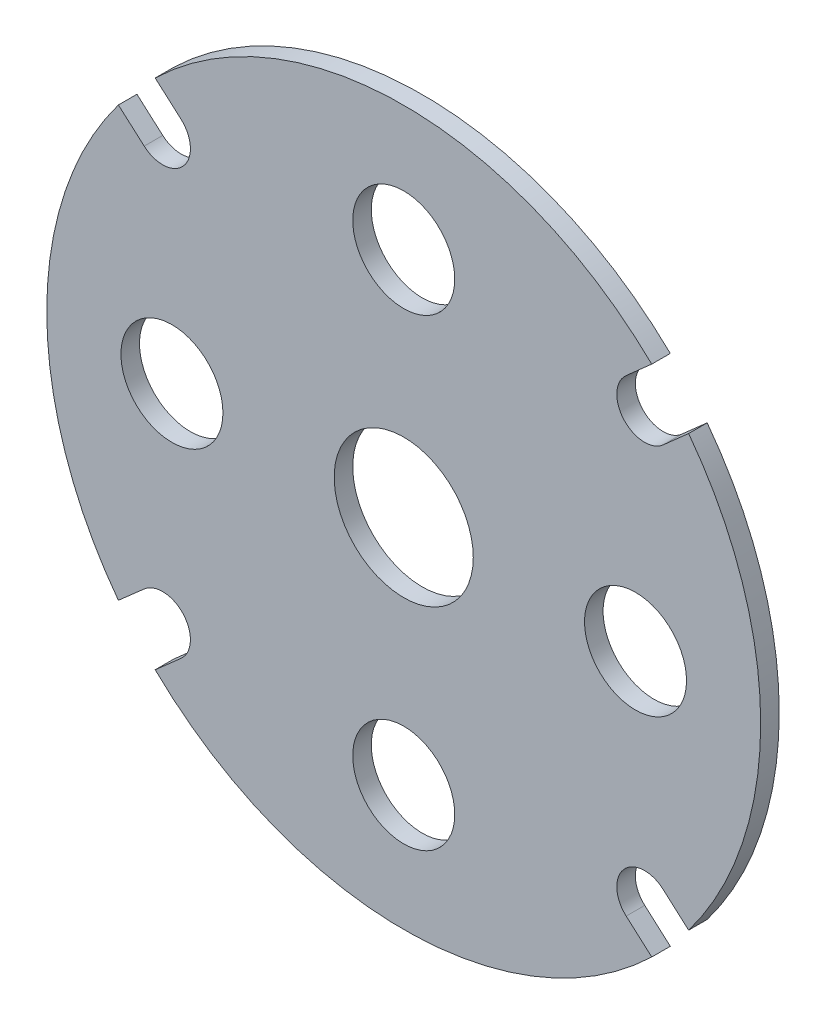
SolidWorks part; units mm, degrees
material "Acrylic (Medium-high impact)"
ref_plane "Front Plane" through (0, 0, 0) normal (0, 0, 1) x (1, 0, 0)
ref_plane "Top Plane" through (0, 0, 0) normal (0, 1, 0) x (1, 0, 0)
ref_plane "Right Plane" through (0, 0, 0) normal (1, 0, 0) x (0, 0, -1)
sketch "Model" plane through (0, 0, 0) normal (0, 0, 1) x (1, 0, 0)
  line L0 (30.7279, -23.1958) -> (27.9693, -20.7537)
  line L1 (26.7508, -27.6884) -> (23.9922, -25.2463)
  line L2 (-30.7735, -23.1353) -> (-27.9907, -20.6815)
  line L3 (-26.8052, -27.6357) -> (-24.0224, -25.1819)
  line L8 (30.7279, 23.1958) -> (27.9693, 20.7537)
  line L9 (26.7508, 27.6884) -> (23.9922, 25.2463)
  line L10 (-30.7735, 23.1353) -> (-27.9907, 20.6815)
  line L11 (-26.8052, 27.6357) -> (-24.0224, 25.1819)
  circle A8 centre (0, 0) radius 7.5
  arc A9 (-26.8052, -27.6357) -> (26.7508, -27.6884) centre (0, 0) ccw
  arc A10 (30.7279, -23.1958) -> (30.7279, 23.1958) centre (0, 0) ccw
  circle A11 centre (-25, 0) radius 5.5
  circle A12 centre (0, 25) radius 5.5
  circle A13 centre (0, -25) radius 5.5
  circle A14 centre (25, 0) radius 5.5
  arc A15 (27.9693, -20.7537) -> (23.9922, -25.2463) centre (25.9808, -23) ccw
  arc A16 (-24.0224, -25.1819) -> (-27.9907, -20.6815) centre (-26.0066, -22.9317) ccw
  arc A26 (23.9922, 25.2463) -> (27.9693, 20.7537) centre (25.9808, 23) ccw
  arc A27 (-27.9907, 20.6815) -> (-24.0224, 25.1819) centre (-26.0066, 22.9317) ccw
  arc A28 (26.7508, 27.6884) -> (-26.8052, 27.6357) centre (0, 0) ccw
  arc A29 (-30.7735, 23.1353) -> (-30.7735, -23.1353) centre (0, 0) ccw
  dimension "D1" = 11
  dimension "D2" = 15
  dimension "D3" = 38.5
  dimension "D4" = 3
  dimension "D5" = 23.9922
  dimension "D6" = 25
  dimension "D7" = 25.9808
  dimension "D8" = 26.7508
  dimension "D9" = 24.0224
  dimension "D10" = 25
  dimension "D11" = 26.0066
  dimension "D12" = 26.8052
  dimension "D13" = 25
  dimension "D14" = 25
extrude "Boss-Extrude1" add sketch "Model" along normal blind 2
